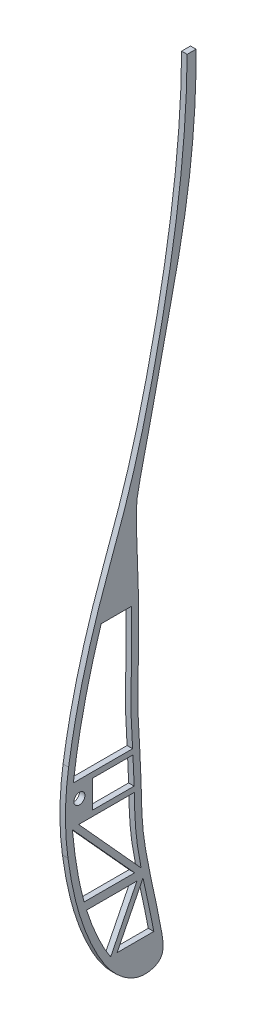
SolidWorks part; units mm, degrees
ref_plane "Front Plane" through (0, 0, 0) normal (0, 0, 1) x (1, 0, 0)
ref_plane "Top Plane" through (0, 0, 0) normal (0, 1, 0) x (1, 0, 0)
ref_plane "Right Plane" through (0, 0, 0) normal (1, 0, 0) x (0, 0, -1)
sketch "rib1" plane through (0, 0, 0) normal (1, 0, 0) x (0, 0, -1)
  line L0 (-71.2313, 530.3957) -> (928.7687, 530.3957) construction
  line L1 (884.1904, 599.9039) -> (887.9745, 599.9039)
  line L2 (856.9345, 370.6416) -> (865.0745, 370.6416)
  line L3 (850.4345, 376.6416) -> (850.4345, 379.6416)
  line L4 (850.4345, 376.6416) -> (850.4345, 373.6416)
  line L5 (840.8063, 376.6416) -> (845.8063, 376.6416) construction
  line L8 (855.8579, 382.6416) -> (843.7452, 382.6416)
  line L9 (855.8579, 382.6416) -> (864.8136, 382.6416)
  line L10 (856.9345, 368.6416) -> (844.7619, 368.6416)
  line L11 (856.9345, 368.6416) -> (865.1127, 368.6416)
  line L12 (866.2204, 340.1291) -> (848.917, 340.1291)
  line L13 (858.3122, 320.8088) -> (858.0269, 320.2668)
  line L14 (848.4203, 343.1291) -> (847.9481, 343.1291)
  line L15 (860.5104, 442.9155) -> (866.5886, 442.9155)
  line L16 (858.0269, 320.2668) -> (873.8862, 320.2668)
  line L17 (855.8579, 318.9992) -> (874.2194, 327.9134) construction
  line L18 (854.766, 321.2482) -> (871.1797, 329.2167) construction
  line L19 (871.1797, 329.2167) -> (873.8862, 320.2668)
  line L20 (843.5049, 367.0528) -> (865.4106, 343.1291)
  line L21 (866.2204, 340.1291) -> (856.8415, 322.3087)
  line L22 (844.7619, 368.6416) -> (867.7752, 343.5082)
  line L23 (868.4574, 340.0851) -> (858.3122, 320.8088)
  line L24 (865.4106, 343.1291) -> (848.4203, 343.1291)
  line L26 (856.9345, 370.6416) -> (850.4345, 370.6416)
  line L27 (850.4345, 370.6416) -> (850.4345, 373.6416)
  line L29 (855.8579, 380.6416) -> (864.9113, 380.6416)
  line L30 (855.8579, 380.6416) -> (850.4345, 380.6416)
  line L31 (850.4345, 380.6416) -> (850.4345, 379.6416)
  circle A0 centre (845.8063, 376.6416) radius 2
  arc A1 (841.0443, 380.5713) -> (847.6718, 415.72) centre (1017.3451, 365.528) cw
  arc A2 (851.2954, 425.5507) -> (861.6081, 456.6454) centre (699.0135, 493.3134) ccw
  arc A3 (862.9829, 461.9026) -> (884.1904, 599.9039) centre (374.0528, 607.6697) ccw
  arc A4 (840.7788, 371.8072) -> (855.8579, 318.9992) centre (950.1899, 374.4922) ccw
  arc A5 (867.6216, 376.9662) -> (872.8022, 332.64) centre (1022.9399, 372.6533) ccw
  arc A6 (867.6216, 376.9662) -> (871.4996, 461.3529) centre (1263.0251, 401.0778) cw
  arc A7 (871.9368, 463.9152) -> (887.9745, 599.9039) centre (-120.6116, 649.9108) ccw
  arc A8 (874.2194, 327.9134) -> (872.8022, 332.64) centre (950.104, 353.2418) cw
  arc A9 (841.0443, 380.5713) -> (840.7788, 371.8072) centre (920.7547, 373.7698) ccw
  arc A10 (851.2954, 425.5507) -> (847.6718, 415.72) centre (924.3857, 393.0268) ccw
  arc A11 (862.9829, 461.9026) -> (861.6081, 456.6454) centre (939.6482, 439.046) ccw
  arc A12 (871.4996, 461.3529) -> (871.9368, 463.9152) centre (950.5681, 449.1804) cw
  arc A13 (843.7452, 382.6416) -> (850.0691, 415.0108) centre (1017.3451, 365.528) cw
  arc A14 (853.5794, 424.5344) -> (850.0691, 415.0108) centre (924.3857, 393.0268) ccw
  arc A15 (853.5794, 424.5344) -> (860.5104, 442.9155) centre (699.0135, 493.3134) ccw
  arc A16 (843.5353, 380.3587) -> (850.0691, 415.0108) centre (1017.3451, 365.528) cw construction
  arc A17 (843.5049, 367.0528) -> (847.9481, 343.1291) centre (950.1899, 374.4922) ccw
  arc A18 (865.0721, 374.4641) -> (865.0745, 370.6416) centre (1022.9399, 372.6533) ccw
  arc A19 (864.962, 379.6766) -> (864.9113, 380.6416) centre (1263.0251, 401.0778) cw
  arc A20 (871.1797, 329.2167) -> (870.3865, 331.9962) centre (950.104, 353.2418) cw
  arc A21 (868.4574, 340.0851) -> (870.3865, 331.9962) centre (1022.9399, 372.6533) ccw
  arc A22 (865.3787, 461.1883) -> (886.6901, 599.8658) centre (374.0528, 607.6697) ccw construction
  arc A23 (865.1195, 376.9245) -> (870.3865, 331.9962) centre (1022.9399, 372.6533) ccw construction
  arc A24 (869.4795, 464.3757) -> (885.4776, 600.0277) centre (-120.6116, 649.9108) ccw construction
  arc A25 (843.278, 371.8685) -> (858.0127, 320.2668) centre (950.1899, 374.4922) ccw construction
  arc A26 (853.5794, 424.5344) -> (864.0469, 456.0955) centre (699.0135, 493.3134) ccw construction
  arc A27 (865.3787, 461.1883) -> (864.0469, 456.0955) centre (939.6482, 439.046) ccw construction
  arc A28 (865.1195, 376.9245) -> (869.0287, 461.7333) centre (1263.0251, 401.0778) cw construction
  arc A29 (869.0287, 461.7333) -> (869.4795, 464.3757) centre (950.5681, 449.1804) cw construction
  arc A30 (848.917, 340.1291) -> (856.8415, 322.3087) centre (950.1899, 374.4922) ccw
  arc A31 (865.1127, 368.6416) -> (867.7752, 343.5082) centre (1022.9399, 372.6533) ccw
  arc A32 (864.8136, 382.6416) -> (866.5886, 442.9155) centre (1263.0251, 401.0778) cw
  arc A33 (865.0721, 374.4641) -> (864.962, 379.6766) centre (785.0773, 375.3817) ccw
  spline S0 degree 3 poles (855.8579, 318.9992) (859.3648, 313.0596) (867.0534, 309.8477) (875.8907, 311.5767) (877.0472, 317.8757) (875.7309, 323.2627) (874.9921, 325.5984) (874.2194, 327.9134) knots 0 0 0 0 0.275026 0.518183 0.708506 0.751927 0.952395 0.952395 0.952395 0.952395
  dimension "D2" = 2.5
  dimension "D1" = 1000
sketch "rib2" plane through (0, 0, 0) normal (1, 0, 0) x (0, 0, -1)
  line L0 (-154.4211, 376.6416) -> (49845.5789, 376.6416) construction
  line L1 (-144.1421, 380.6416) -> (49855.8579, 380.6416) construction
  line L2 (-143.0655, 370.6416) -> (49856.9345, 370.6416) construction
  line L3 (782.8933, 343.3859) -> (760.3563, 368.2109)
  line L4 (-143.0655, 368.6416) -> (49856.9345, 368.6416) construction
  line L5 (-144.1421, 382.6416) -> (49855.8579, 382.6416) construction
  line L6 (785.2354, 343.762) -> (762.6647, 368.6416)
  line L7 (764.6298, 343.3859) -> (782.8933, 343.3859)
  line L8 (783.7374, 340.3859) -> (774.2204, 321.3554)
  line L9 (767.5719, 380.6416) -> (767.5719, 370.6416)
  line L10 (767.5719, 370.6416) -> (782.7291, 370.6416)
  line L11 (767.5719, 380.6416) -> (782.2855, 380.6416)
  line L12 (765.5126, 340.3859) -> (783.7374, 340.3859)
  line L13 (762.6647, 368.6416) -> (782.7755, 368.6416)
  line L14 (776.5435, 321.5294) -> (789.8459, 321.5294)
  line L15 (760.7138, 382.6416) -> (782.1585, 382.6416)
  line L16 (770.7866, 427.4918) -> (781.8144, 427.4918)
  line L17 (801.9062, 590.4081) -> (805.115, 590.4081)
  line L18 (757.9166, 376.6416) -> (762.9166, 376.6416) construction
  line L20 (785.9296, 340.298) -> (776.5435, 321.5294)
  circle A0 centre (762.9166, 376.6416) radius 2
  arc A1 (758.9972, 388.4269) -> (758.7602, 360.0657) centre (857.8646, 373.419) ccw
  spline S0 degree 3 poles (758.7602, 360.0657) (759.4545, 354.9126) (761.6392, 342.918) (767.6025, 326.3565) (776.3644, 313.1833) (785.8807, 308.842) (791.3139, 310.6103) (793.0754, 312.9879) (793.3375, 316.1077) (791.0414, 329.6431) (787.956, 341.1966) (785.2042, 359.6207) (785.4538, 372.9971) (783.4315, 397.4301) (785.2476, 420.7625) (783.0535, 455.8097) (784.4694, 464.3867) (788.1328, 479.2935) (793.2428, 503.9805) (802.5401, 542.6054) (805.2587, 572.3941) (805.115, 590.4081) knots 0.028705 0.028705 0.028705 0.028705 0.059247 0.100348 0.1322 0.149146 0.158796 0.160734 0.16766 0.175847 0.234409 0.24607 0.285136 0.310616 0.385264 0.441942 0.454033 0.506165 0.624061 0.777474 1 1 1 1
  spline S1 degree 3 poles (801.9062, 590.4081) (801.6966, 560.1521) (794.9988, 516.4373) (781.9369, 464.9221) (769.955, 434.3358) (762.9603, 410.299) (759.9193, 394.5015) (758.9972, 388.4269) knots 0 0 0 0 0.408823 0.598513 0.719262 0.854061 0.937351 0.937351 0.937351 0.937351
  spline S2 degree 3 poles (760.3563, 368.2109) (760.6455, 365.1083) (761.2971, 359.3998) (762.6856, 351.2079) (763.8909, 346.0643) (764.604, 343.4789) (764.6298, 343.3859) knots 0.01313 0.01313 0.01313 0.01313 0.031626 0.047245 0.062864 0.063447 0.063447 0.063447 0.063447
  spline S3 degree 3 poles (765.5126, 340.3859) (765.9421, 339.0082) (767.2255, 335.1967) (769.2617, 330.2911) (771.6089, 325.6402) (773.0967, 323.06) (774.0043, 321.6748) (774.2204, 321.3554) knots 0.069751 0.069751 0.069751 0.069751 0.078483 0.094102 0.101912 0.109721 0.112105 0.112105 0.112105 0.112105
  spline S5 degree 3 poles (782.7291, 370.6416) (782.7064, 371.5634) (782.6438, 373.8426) (782.4996, 377.1608) (782.3523, 379.5799) (782.2855, 380.6416) knots 0.276245 0.276245 0.276245 0.276245 0.281529 0.289339 0.295445 0.295445 0.295445 0.295445
  spline S6 degree 3 poles (789.8459, 321.5294) (789.8142, 321.6995) (789.7504, 322.0389) (789.4577, 323.5807) (788.9295, 326.2404) (788.1496, 329.9526) (787.3325, 333.724) (786.5882, 337.1579) (786.1256, 339.3494) (785.9296, 340.298) knots 0.178918 0.178918 0.178918 0.178918 0.179894 0.18087 0.187816 0.195625 0.203435 0.211244 0.21717 0.21717 0.21717 0.21717
  spline S7 degree 3 poles (785.2354, 343.762) (784.9117, 345.4358) (784.3695, 348.4126) (783.6834, 352.846) (783.0923, 358.3507) (782.8866, 363.6197) (782.8011, 367.501) (782.7755, 368.6416) knots 0.224345 0.224345 0.224345 0.224345 0.234672 0.242482 0.250291 0.26591 0.27243 0.27243 0.27243 0.27243
  spline S8 degree 3 poles (782.1585, 382.6416) (782.0098, 384.985) (781.5323, 392.7288) (781.6016, 402.5045) (781.8121, 413.0284) (781.8895, 420.0466) (781.8563, 425.0079) (781.8229, 427.0307) (781.8144, 427.4918) knots 0.299279 0.299279 0.299279 0.299279 0.312767 0.344005 0.359624 0.375243 0.383052 0.385336 0.385336 0.385336 0.385336
  spline S9 degree 3 poles (770.7866, 427.4918) (769.4671, 423.3387) (766.9647, 414.7701) (763.3804, 399.8515) (761.5251, 389.0141) (760.7138, 382.6416) knots 0.752168 0.752168 0.752168 0.752168 0.811773 0.874217 0.962264 0.962264 0.962264 0.962264
  point P26 (765.5126, 340.3859)
  point P30 (764.6298, 343.3859)
  point P35 (774.2204, 321.3554)
  point P36 (789.8459, 321.5294)
  point P37 (785.9296, 340.298)
  point P39 (760.3563, 368.2109)
  point P40 (760.0729, 371.4986)
  dimension "D1" = 100
sketch "Sketch5" plane through (0, 0, 0) normal (1, 0, 0) x (0, 0, -1)
  line L0 (-200154.4211, 376.6416) -> (249845.5789, 376.6416) construction
  line L1 (693.317, 322.1015) -> (707.0464, 322.1015)
  line L2 (695.5696, 447.1101) -> (698.3736, 447.1101)
  line L3 (698.6642, 410.7316) -> (681.8197, 410.7316)
  line L4 (698.7261, 405.5878) -> (680.4847, 405.5878)
  line L5 (677.0801, 382.6416) -> (699.3215, 382.6416)
  line L7 (699.7026, 368.6416) -> (679.4803, 368.6416)
  line L8 (-200143.0655, 368.6416) -> (249856.9345, 368.6416) construction
  line L9 (674.1545, 376.6416) -> (679.1545, 376.6416) construction
  line L10 (684.2181, 380.6416) -> (684.2181, 370.6416)
  line L11 (-200144.1421, 380.6416) -> (249855.8579, 380.6416) construction
  line L12 (-200143.0655, 370.6416) -> (249856.9345, 370.6416) construction
  line L13 (684.2181, 370.6416) -> (699.6248, 370.6416)
  line L14 (702.2048, 368.6416) -> (702.335, 365.9116)
  line L15 (699.3639, 380.6416) -> (684.2181, 380.6416)
  line L16 (708.485, 312.754) -> (708.6651, 312.9152)
  line L17 (706.7921, 314.6987) -> (706.9599, 314.7434)
  line L18 (699.8434, 365.7077) -> (699.7071, 368.5354)
  line L19 (682.1263, 343.4207) -> (681.5591, 343.4207)
  line L20 (700.6109, 340.4181) -> (682.6985, 340.4181)
  line L21 (699.3639, 380.6416) -> (699.6248, 370.6416)
  line L22 (705.0572, 343.4207) -> (704.8181, 343.4207)
  line L23 (716.7384, 582.0418) -> (720.2752, 582.0418)
  line L24 (693.317, 322.1015) -> (702.7962, 340.2834)
  line L25 (702.2445, 343.7103) -> (679.4803, 368.6416)
  line L26 (691.5466, 323.0319) -> (700.6109, 340.4181)
  line L28 (699.8006, 343.4207) -> (682.1263, 343.4207)
  line L32 (699.8006, 343.4207) -> (677.0187, 368.3713)
  circle A0 centre (679.1545, 376.6416) radius 2
  spline S0 degree 3 poles (674.1545, 376.6416) (674.6209, 363.9047) (675.4244, 348.9718) (687.0005, 324.6734) (691.715, 318.3055) (697.5054, 311.9056) (699.9912, 310.5046) (704.8962, 310.5781) (707.1739, 311.6254) (708.485, 312.754) knots 0 0 0 0 0.082297 0.137777 0.177735 0.177735 0.194632 0.194632 0.2043 0.2043 0.2043 0.2043
  spline S1 degree 3 poles (716.7384, 582.0418) (716.9491, 569.6586) (716.384, 531.2528) (699.2016, 484.7456) (692.8166, 441.1757) (677.838, 413.403) (675.0171, 391.1698) (674.1545, 376.6416) knots 0 0 0 0 0.169562 0.555938 0.689283 0.791056 1 1 1 1
  spline S2 degree 3 poles (702.2445, 343.7103) (702.1641, 344.2407) (701.7657, 346.9448) (701.1382, 351.8745) (700.5581, 357.5193) (700.1402, 362.1447) (699.9401, 364.5255) (699.8434, 365.7077) knots 0.317112 0.317112 0.317112 0.317112 0.32289 0.346516 0.370142 0.381955 0.393768 0.393768 0.393768 0.393768
  spline S4 degree 3 poles (702.2048, 368.6416) (701.8669, 376.5926) (701.8555, 384.7425) (701.1266, 402.784) (701.1396, 431.7405) (700.5544, 456.9254) (705.1133, 487.005) (717.5576, 525.1697) (721.078, 562.1394) (720.2752, 582.0418) knots 0.402967 0.402967 0.402967 0.402967 0.483086 0.483086 0.591391 0.687653 0.687653 0.844633 1 1 1 1
  spline S5 degree 3 poles (699.3215, 382.6416) (699.3024, 383.5334) (699.2425, 386.2646) (699.1476, 389.8671) (699.0014, 393.4021) (698.878, 397.2735) (698.7899, 401.3622) (698.7401, 404.5905) (698.7261, 405.5878) knots 0.449941 0.449941 0.449941 0.449941 0.458939 0.477596 0.486925 0.496254 0.514911 0.523067 0.523067 0.523067 0.523067
  spline S6 degree 3 poles (699.7071, 368.5354) (699.7056, 368.5708) (699.7041, 368.6062) (699.7026, 368.6416) knots 0.402967 0.402967 0.402967 0.402967 0.40332 0.40332 0.40332 0.40332
  spline S7 degree 3 poles (682.6985, 340.4181) (683.0121, 339.6321) (683.9949, 337.2558) (685.7648, 333.3639) (687.9735, 329.011) (689.7493, 325.8616) (690.8989, 324.0094) (691.3927, 323.2607) (691.5466, 323.0319) knots 0.095831 0.095831 0.095831 0.095831 0.10215 0.114919 0.127687 0.140456 0.14684 0.149678 0.149678 0.149678 0.149678
  spline S8 degree 3 poles (677.0187, 368.3713) (677.0192, 368.3626) (677.0681, 367.4934) (677.2257, 364.9551) (677.5669, 360.9606) (678.1637, 356.4034) (679.0103, 351.9539) (680.1158, 347.6804) (681.0683, 344.7879) (681.5591, 343.4207) knots 0.019088 0.019088 0.019088 0.019088 0.019153 0.025537 0.038306 0.051075 0.063844 0.076612 0.087747 0.087747 0.087747 0.087747
  spline S9 degree 3 poles (708.6651, 312.9152) (709.0596, 313.2832) (711.3268, 316.9807) (705.4793, 334.2076) (703.6294, 350.0939) (702.335, 365.9116) knots 0.204759 0.204759 0.204759 0.204759 0.207895 0.236848 0.393768 0.393768 0.393768 0.393768
  spline S10 degree 3 poles (676.659, 376.6416) (676.6584, 376.6321) (676.6578, 376.6225) (676.6573, 376.613) knots 0.999862 0.999862 0.999862 0.999862 1 1 1 1
  spline S11 degree 3 poles (707.0464, 322.1015) (707.0052, 322.2371) (706.9227, 322.5094) (706.5342, 323.8003) (705.9077, 326.017) (705.0863, 329.1749) (704.0811, 333.4582) (703.3421, 337.155) (702.8797, 339.7948) (702.7962, 340.2834) knots 0.237993 0.237993 0.237993 0.237993 0.239469 0.240946 0.252011 0.263824 0.275637 0.299263 0.304623 0.304623 0.304623 0.304623
  spline S12 degree 3 poles (680.4847, 405.5878) (680.2388, 404.5378) (679.0822, 399.2686) (677.9122, 391.5905) (677.2696, 384.9533) (677.0801, 382.6416) knots 0.859357 0.859357 0.859357 0.859357 0.875 0.9375 0.970921 0.970921 0.970921 0.970921
  spline S13 degree 3 poles (698.6642, 410.7316) (698.6438, 412.7052) (698.5832, 419.5769) (698.503, 431.741) (698.3426, 441.7088) (698.3711, 446.7739) (698.3736, 447.1101) knots 0.536769 0.536769 0.536769 0.536769 0.552225 0.58954 0.626855 0.629511 0.629511 0.629511 0.629511
  spline S15 degree 3 poles (695.5696, 447.1101) (695.4451, 446.6155) (694.7557, 443.952) (693.3092, 439.1408) (690.7575, 432.8707) (687.9819, 426.8359) (685.294, 420.8884) (683.2818, 415.5566) (682.219, 412.126) (681.8197, 410.7316) knots 0.649129 0.649129 0.649129 0.649129 0.65625 0.6875 0.71875 0.75 0.78125 0.8125 0.833615 0.833615 0.833615 0.833615
sketch "Sketch6" plane through (0, 0, 0) normal (1, 0, 0) x (0, 0, -1)
  line L0 (-200154.4211, 376.6416) -> (249845.5789, 376.6416) construction
  line L1 (594.2077, 382.6416) -> (615.9917, 382.6416)
  line L2 (-200144.1421, 382.6416) -> (249855.8579, 382.6416) construction
  line L3 (617.0002, 368.6416) -> (597.1315, 368.6416)
  line L4 (-200143.0655, 368.6416) -> (249856.9345, 368.6416) construction
  line L7 (609.0006, 321.5886) -> (608.931, 321.4458)
  line L8 (610.7981, 320.7115) -> (610.2002, 319.4863)
  line L9 (594.4326, 368.6416) -> (594.0581, 368.6416)
  line L11 (594.4326, 368.6416) -> (617.3118, 343.3906)
  line L12 (618.1756, 340.3906) -> (609.0006, 321.5886)
  line L13 (597.1315, 368.6416) -> (619.7239, 343.7071)
  line L23 (620.3211, 340.2268) -> (610.7981, 320.7115)
  line L28 (618.1756, 340.3906) -> (599.7563, 340.3906)
  line L29 (617.3118, 343.3906) -> (598.7382, 343.3906)
  arc A0 (610.8725, 452.2517) -> (615.4146, 451.3048) centre (613.0575, 451.3657) cw
  spline S0 degree 3 poles (591.4519, 376.6416) (590.8724, 355.6832) (598.0127, 330.747) (614.7237, 309.0913) (626.4002, 308.0944) (627.1878, 324.0074) (622.1741, 339.2467) (620.5135, 359.7877) (618.195, 380.0068) (618.3402, 403.8303) (616.7499, 433.3564) (618.9592, 474.5213) (631.6465, 520.1908) (636.0177, 556.3417) (635.098, 572.5915) knots 0 0 0 0 0.181753 0.211103 0.236632 0.255743 0.327686 0.385848 0.430346 0.504499 0.591378 0.686471 0.859586 1 1 1 1
  spline S1 degree 3 poles (632.3767, 572.5915) (632.331, 559.797) (630.7518, 538.4728) (623.6454, 509.5847) (617.1086, 483.6159) (609.1878, 456.4292) (602.6277, 431.1093) (594.4581, 405.0022) (591.6906, 387.7261) (591.4519, 376.6416) knots 0 0 0 0 0.191351 0.317516 0.443871 0.591483 0.740453 0.834547 1 1 1 1
  spline S2 degree 3 poles (619.7239, 343.7071) (619.5881, 344.5842) (619.2022, 347.2732) (618.6764, 351.7986) (618.1443, 357.2765) (617.6179, 362.6875) (617.2186, 366.4692) (617.0187, 368.4566) (617.0002, 368.6416) knots 0.33611 0.33611 0.33611 0.33611 0.343735 0.359361 0.374986 0.390612 0.406237 0.40784 0.40784 0.40784 0.40784
  spline S3 degree 3 poles (599.7563, 340.3906) (599.7882, 340.3011) (600.4188, 338.5434) (601.7436, 335.154) (603.9399, 330.3213) (606.3333, 325.742) (608.0626, 322.8243) (608.931, 321.4458) knots 0.108518 0.108518 0.108518 0.108518 0.109355 0.124981 0.140606 0.156231 0.170688 0.170688 0.170688 0.170688
  spline S4 degree 3 poles (610.8725, 452.2517) (610.269, 449.893) (608.8998, 444.6758) (606.7371, 436.6294) (604.5222, 428.0779) (602.3578, 419.4861) (600.0573, 410.8763) (597.5945, 402.3898) (595.6103, 393.891) (594.6157, 387.2692) (594.2744, 383.5122) (594.2077, 382.6416) knots 0.448611 0.448611 0.448611 0.448611 0.500019 0.562521 0.625024 0.687526 0.750029 0.812531 0.875033 0.937536 0.956374 0.956374 0.956374 0.956374
  spline S5 degree 3 poles (594.0581, 368.6416) (594.1057, 367.7673) (594.4036, 363.3735) (595.4715, 355.4692) (597.3077, 347.9625) (598.5477, 343.9825) (598.7382, 343.3906) knots 0.023466 0.023466 0.023466 0.023466 0.031229 0.062479 0.09373 0.09921 0.09921 0.09921 0.09921
  spline S6 degree 3 poles (610.2002, 319.4863) (610.3292, 319.2923) (610.9476, 318.3692) (612.075, 316.7416) (613.5938, 314.8775) (615.268, 313.3623) (617.1903, 312.2288) (619.6971, 311.4612) (621.7209, 311.3604) (622.8414, 311.5923) (623.3355, 311.851) (623.4973, 312.0037) (623.7734, 312.4798) (624.0122, 313.3728) (624.1915, 314.9548) (624.1754, 317.4057) (624.0268, 320.2009) (623.7469, 322.9038) (623.3647, 325.5305) (622.9006, 328.1059) (622.2032, 331.5008) (621.2956, 335.4836) (620.6086, 338.7108) (620.3211, 340.2268) knots 0.177597 0.177597 0.177597 0.177597 0.179669 0.187482 0.195295 0.203107 0.21092 0.218733 0.226545 0.230452 0.234358 0.238264 0.242171 0.246077 0.249983 0.257796 0.265609 0.273421 0.281234 0.289047 0.296859 0.312485 0.325931 0.325931 0.325931 0.325931
  spline S7 degree 3 poles (615.9917, 382.6416) (615.8973, 385.0577) (615.7504, 391.1062) (615.6642, 400.7347) (615.3415, 411.5075) (614.9499, 422.3472) (614.7472, 433.2494) (614.9316, 442.9184) (615.2536, 448.9371) (615.4146, 451.3048) knots 0.447995 0.447995 0.447995 0.447995 0.468738 0.499989 0.53124 0.56249 0.593741 0.624992 0.645293 0.645293 0.645293 0.645293
extrude "Boss-Extrude5" add sketch "rib2" along normal blind 2
equation "\"1000mmm\"=767.321"
